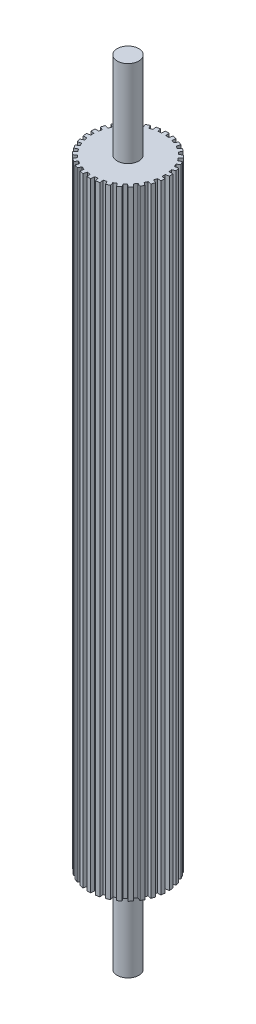
SolidWorks part; units mm, degrees
ref_plane "Front Plane" through (0, 0, 0) normal (0, 0, 1) x (1, 0, 0)
ref_plane "Top Plane" through (0, 0, 0) normal (0, 1, 0) x (1, 0, 0)
ref_plane "Right Plane" through (0, 0, 0) normal (1, 0, 0) x (0, 0, -1)
sketch "Sketch2" plane through (0, 0, 0) normal (0, 1, 0) x (1, 0, 0)
  line L1 (-0.7753, 12.6763) -> (-0.6703, 13.9539)
  line L2 (0.7753, 12.6763) -> (0.6703, 13.9539)
  line L3 (1.8772, 12.5605) -> (2.2456, 13.7883)
  line L4 (3.3939, 12.2381) -> (3.5568, 13.5096)
  line L5 (4.4476, 11.8957) -> (5.0633, 13.0201)
  line L6 (5.8642, 11.265) -> (6.2879, 12.4749)
  line L7 (6.8237, 10.7111) -> (7.6597, 11.6829)
  line L8 (8.0782, 9.7996) -> (8.7442, 10.895)
  line L9 (8.9015, 9.0583) -> (9.9213, 9.8351)
  line L10 (9.9391, 7.9059) -> (10.8183, 8.8389)
  line L11 (10.5903, 7.0096) -> (11.7493, 7.5574)
  line L12 (11.3657, 5.6667) -> (12.4196, 6.3965)
  line L13 (11.8163, 4.6546) -> (13.0638, 4.9494)
  line L14 (12.2955, 3.1798) -> (13.4781, 3.6745)
  line L15 (12.5258, 2.0961) -> (13.8074, 2.1252)
  line L16 (12.6879, 0.554) -> (13.9475, 0.792)
  line L17 (12.6879, -0.554) -> (13.9475, -0.792)
  line L18 (12.5258, -2.0961) -> (13.8074, -2.1252)
  line L19 (12.2955, -3.1798) -> (13.4781, -3.6745)
  line L20 (11.8163, -4.6546) -> (13.0638, -4.9494)
  line L21 (11.3657, -5.6667) -> (12.4196, -6.3965)
  line L22 (10.5903, -7.0096) -> (11.7493, -7.5574)
  line L23 (9.9391, -7.9059) -> (10.8183, -8.8389)
  line L24 (8.9015, -9.0583) -> (9.9213, -9.8351)
  line L25 (8.0782, -9.7996) -> (8.7442, -10.895)
  line L26 (6.8237, -10.7111) -> (7.6597, -11.6829)
  line L27 (5.8642, -11.265) -> (6.2879, -12.4749)
  line L28 (4.4476, -11.8957) -> (5.0633, -13.0201)
  line L29 (3.3939, -12.2381) -> (3.5568, -13.5096)
  line L30 (1.8772, -12.5605) -> (2.2456, -13.7883)
  line L31 (0.7753, -12.6763) -> (0.6703, -13.9539)
  line L32 (-0.7753, -12.6763) -> (-0.6703, -13.9539)
  line L33 (-1.8772, -12.5605) -> (-2.2456, -13.7883)
  line L34 (-3.3939, -12.2381) -> (-3.5568, -13.5096)
  line L35 (-4.4476, -11.8957) -> (-5.0633, -13.0201)
  line L36 (-5.8642, -11.265) -> (-6.2879, -12.4749)
  line L37 (-6.8237, -10.7111) -> (-7.6597, -11.6829)
  line L38 (-8.0782, -9.7996) -> (-8.7442, -10.895)
  line L39 (-8.9015, -9.0583) -> (-9.9213, -9.8351)
  line L40 (-9.9391, -7.9059) -> (-10.8183, -8.8389)
  line L41 (-10.5903, -7.0096) -> (-11.7493, -7.5574)
  line L42 (-11.3657, -5.6667) -> (-12.4196, -6.3965)
  line L43 (-11.8163, -4.6546) -> (-13.0638, -4.9494)
  line L44 (-12.2955, -3.1798) -> (-13.4781, -3.6745)
  line L45 (-12.5258, -2.0961) -> (-13.8074, -2.1252)
  line L46 (-12.6879, -0.554) -> (-13.9475, -0.792)
  line L47 (-12.6879, 0.554) -> (-13.9475, 0.792)
  line L48 (-12.5258, 2.0961) -> (-13.8074, 2.1252)
  line L49 (-12.2955, 3.1798) -> (-13.4781, 3.6745)
  line L50 (-11.8163, 4.6546) -> (-13.0638, 4.9494)
  line L51 (-11.3657, 5.6667) -> (-12.4196, 6.3965)
  line L52 (-10.5903, 7.0096) -> (-11.7493, 7.5574)
  line L53 (-9.9391, 7.9059) -> (-10.8183, 8.8389)
  line L54 (-8.9015, 9.0583) -> (-9.9213, 9.8351)
  line L55 (-8.0782, 9.7996) -> (-8.7442, 10.895)
  line L56 (-6.8237, 10.7111) -> (-7.6597, 11.6829)
  line L57 (-5.8642, 11.265) -> (-6.2879, 12.4749)
  line L58 (-4.4476, 11.8957) -> (-5.0633, 13.0201)
  line L59 (-3.3939, 12.2381) -> (-3.5568, 13.5096)
  line L60 (-1.8772, 12.5605) -> (-2.2456, 13.7883)
  arc A0 (-2.2456, 13.7883) -> (-3.5568, 13.5096) centre (0, 0) ccw
  arc A1 (-0.7753, 12.6763) -> (-1.8772, 12.5605) centre (0, 0) ccw
  arc A3 (-3.3939, 12.2381) -> (-4.4476, 11.8957) centre (0, 0) ccw
  arc A4 (-5.0633, 13.0201) -> (-6.2879, 12.4749) centre (0, 0) ccw
  arc A5 (-5.8642, 11.265) -> (-6.8237, 10.7111) centre (0, 0) ccw
  arc A6 (-7.6597, 11.6829) -> (-8.7442, 10.895) centre (0, 0) ccw
  arc A7 (-8.0782, 9.7996) -> (-8.9015, 9.0583) centre (0, 0) ccw
  arc A8 (-9.9213, 9.8351) -> (-10.8183, 8.8389) centre (0, 0) ccw
  arc A9 (-9.9391, 7.9059) -> (-10.5903, 7.0096) centre (0, 0) ccw
  arc A10 (-11.7493, 7.5574) -> (-12.4196, 6.3965) centre (0, 0) ccw
  arc A11 (-11.3657, 5.6667) -> (-11.8163, 4.6546) centre (0, 0) ccw
  arc A12 (-13.0638, 4.9494) -> (-13.4781, 3.6745) centre (0, 0) ccw
  arc A13 (-12.2955, 3.1798) -> (-12.5258, 2.0961) centre (0, 0) ccw
  arc A14 (-13.8074, 2.1252) -> (-13.9475, 0.792) centre (0, 0) ccw
  arc A15 (-12.6879, 0.554) -> (-12.6879, -0.554) centre (0, 0) ccw
  arc A16 (-13.9475, -0.792) -> (-13.8074, -2.1252) centre (0, 0) ccw
  arc A17 (-12.5258, -2.0961) -> (-12.2955, -3.1798) centre (0, 0) ccw
  arc A18 (-13.4781, -3.6745) -> (-13.0638, -4.9494) centre (0, 0) ccw
  arc A19 (-11.8163, -4.6546) -> (-11.3657, -5.6667) centre (0, 0) ccw
  arc A20 (-12.4196, -6.3965) -> (-11.7493, -7.5574) centre (0, 0) ccw
  arc A21 (-10.5903, -7.0096) -> (-9.9391, -7.9059) centre (0, 0) ccw
  arc A22 (-10.8183, -8.8389) -> (-9.9213, -9.8351) centre (0, 0) ccw
  arc A23 (-8.9015, -9.0583) -> (-8.0782, -9.7996) centre (0, 0) ccw
  arc A24 (-8.7442, -10.895) -> (-7.6597, -11.6829) centre (0, 0) ccw
  arc A25 (-6.8237, -10.7111) -> (-5.8642, -11.265) centre (0, 0) ccw
  arc A26 (-6.2879, -12.4749) -> (-5.0633, -13.0201) centre (0, 0) ccw
  arc A27 (-4.4476, -11.8957) -> (-3.3939, -12.2381) centre (0, 0) ccw
  arc A28 (-3.5568, -13.5096) -> (-2.2456, -13.7883) centre (0, 0) ccw
  arc A29 (-1.8772, -12.5605) -> (-0.7753, -12.6763) centre (0, 0) ccw
  arc A30 (-0.6703, -13.9539) -> (0.6703, -13.9539) centre (0, 0) ccw
  arc A31 (0.7753, -12.6763) -> (1.8772, -12.5605) centre (0, 0) ccw
  arc A32 (2.2456, -13.7883) -> (3.5568, -13.5096) centre (0, 0) ccw
  arc A33 (3.3939, -12.2381) -> (4.4476, -11.8957) centre (0, 0) ccw
  arc A34 (5.0633, -13.0201) -> (6.2879, -12.4749) centre (0, 0) ccw
  arc A35 (5.8642, -11.265) -> (6.8237, -10.7111) centre (0, 0) ccw
  arc A36 (7.6597, -11.6829) -> (8.7442, -10.895) centre (0, 0) ccw
  arc A37 (8.0782, -9.7996) -> (8.9015, -9.0583) centre (0, 0) ccw
  arc A38 (9.9213, -9.8351) -> (10.8183, -8.8389) centre (0, 0) ccw
  arc A39 (9.9391, -7.9059) -> (10.5903, -7.0096) centre (0, 0) ccw
  arc A40 (11.7493, -7.5574) -> (12.4196, -6.3965) centre (0, 0) ccw
  arc A41 (11.3657, -5.6667) -> (11.8163, -4.6546) centre (0, 0) ccw
  arc A42 (13.0638, -4.9494) -> (13.4781, -3.6745) centre (0, 0) ccw
  arc A43 (12.2955, -3.1798) -> (12.5258, -2.0961) centre (0, 0) ccw
  arc A44 (13.8074, -2.1252) -> (13.9475, -0.792) centre (0, 0) ccw
  arc A45 (12.6879, -0.554) -> (12.6879, 0.554) centre (0, 0) ccw
  arc A46 (13.9475, 0.792) -> (13.8074, 2.1252) centre (0, 0) ccw
  arc A47 (12.5258, 2.0961) -> (12.2955, 3.1798) centre (0, 0) ccw
  arc A48 (13.4781, 3.6745) -> (13.0638, 4.9494) centre (0, 0) ccw
  arc A49 (0.6703, 13.9539) -> (-0.6703, 13.9539) centre (0, 0) ccw
  arc A50 (3.5568, 13.5096) -> (2.2456, 13.7883) centre (0, 0) ccw
  arc A51 (6.2879, 12.4749) -> (5.0633, 13.0201) centre (0, 0) ccw
  arc A52 (8.7442, 10.895) -> (7.6597, 11.6829) centre (0, 0) ccw
  arc A53 (1.8772, 12.5605) -> (0.7753, 12.6763) centre (0, 0) ccw
  arc A54 (4.4476, 11.8957) -> (3.3939, 12.2381) centre (0, 0) ccw
  arc A55 (6.8237, 10.7111) -> (5.8642, 11.265) centre (0, 0) ccw
  arc A56 (8.9015, 9.0583) -> (8.0782, 9.7996) centre (0, 0) ccw
  arc A57 (10.5903, 7.0096) -> (9.9391, 7.9059) centre (0, 0) ccw
  arc A58 (10.8183, 8.8389) -> (9.9213, 9.8351) centre (0, 0) ccw
  arc A59 (12.4196, 6.3965) -> (11.7493, 7.5574) centre (0, 0) ccw
  arc A60 (11.8163, 4.6546) -> (11.3657, 5.6667) centre (0, 0) ccw
  point P129 (0, 0)
  dimension "D1" = 30
extrude "Boss-Extrude1" add sketch "Sketch2" along normal blind 211.1375 contours L39 A22 L40 A21 L41 A20 L42 A19 L43 A18 L44 A17 L45 A16 L46 A15 L47 A14 L48 A13 L49 A12 L50 A11 L51 A10 L52 A9 L53 A8 L54 A7 L55 A6 L56 A5 L57 A4 L58 A3 L59 A0 L60 A1 L1 A49 L2 A53 L3 A50 L4 A54 L5 A51 L6 A55 L7 A52 L8 A56 L9 A58 L10 A57 L11 A59 L12 A60 L13 A48 L14 A47 L15 A46 L16 A45 L17 A44 L18 A43 L19 A42 L20 A41 L21 A40 L22 A39 L23 A38 L24 A37 L25 A36 L26 A35 L27 A34 L28 A33 L29 A32 L30 A31 L31 A30 L32 A29 L33 A28 L34 A27 L35 A26 L36 A25 L37 A24 L38 A23
scale "Scale2" scale about centroid uniform scaling no x scale factor 0.96 y scale factor 1 z scale factor 0.96
sketch "Sketch3" plane through (0, 211.1375, 0) normal (0, 1, 0) x (1, 0, 0)
  circle A0 centre (0, 0) radius 3.6805
  dimension "D1" = 7.3609
extrude "Boss-Extrude2" add sketch "Sketch3" along normal blind 29.5593
sketch "Sketch4" plane through (0, 0, 0) normal (0, -1, 0) x (-1, 0, 0)
  circle A0 centre (0, 0) radius 3.6805
  dimension "D1" = 7.3609
extrude "Boss-Extrude3" add sketch "Sketch4" along normal blind 29.5593
